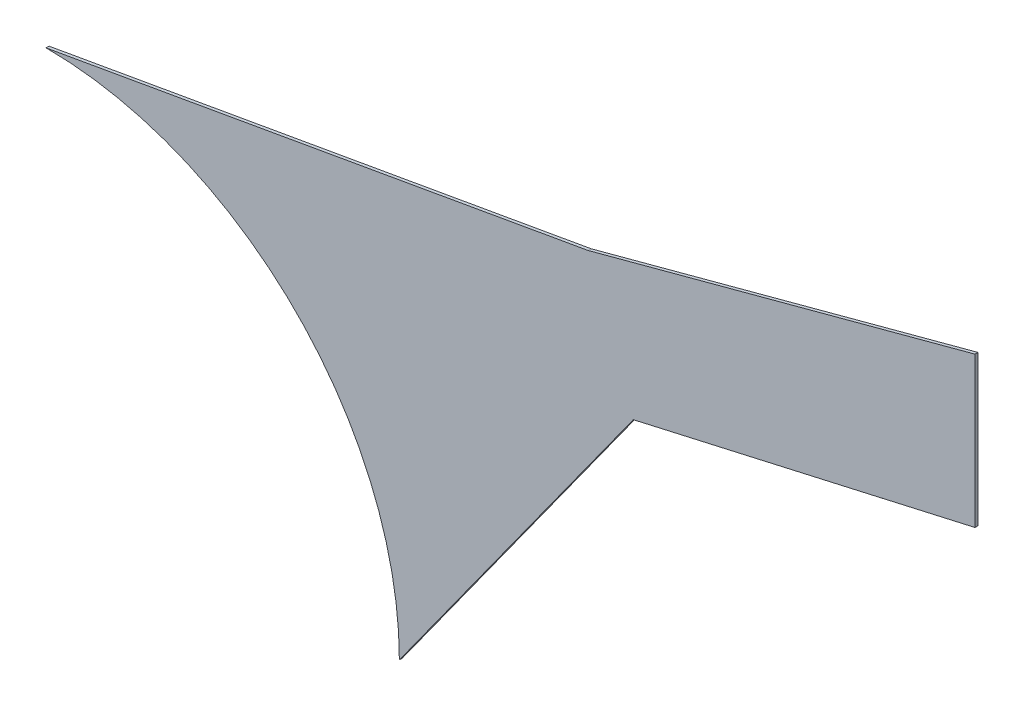
SolidWorks part; units mm, degrees
material "Plain Carbon Steel"
ref_plane "Front Plane" through (0, 0, 0) normal (0, 0, 1) x (1, 0, 0)
ref_plane "Top Plane" through (0, 0, 0) normal (0, 1, 0) x (1, 0, 0)
ref_plane "Right Plane" through (0, 0, 0) normal (1, 0, 0) x (0, 0, -1)
sketch "Sketch1" plane through (0, 0, 0) normal (0, 0, 1) x (1, 0, 0)
  line L0 (0, 179.3189) -> (275.1553, 227.8362)
  line L4 (298.0318, 164.9166) -> (179.3189, 0)
  line L10 (0, 0) -> (0, 179.3189) construction
  line L12 (0, 0) -> (179.3189, 0) construction
  line L13 (298.0318, 164.9166) -> (471.4314, 204.2283)
  line L14 (471.4314, 204.2283) -> (471.4314, 280.4283)
  line L15 (471.4314, 280.4283) -> (275.1553, 227.8362)
  circle A0 centre (0, 0) radius 179.3189 construction
  arc A2 (0, 179.3189) -> (179.3189, 0) centre (0, 0) cw
  point P3 (0, 0)
  dimension "D1" = 358.6378
  dimension "D6" = 260
  dimension "D2" = 279.4
  dimension "D3" = 203.2
  dimension "D4" = 76.2
  dimension "D5" = 203.2
  dimension "D7" = 177.8
  dimension "D8" = 175
extrude "Boss-Extrude1" add sketch "Sketch1" along normal blind 1.5189
